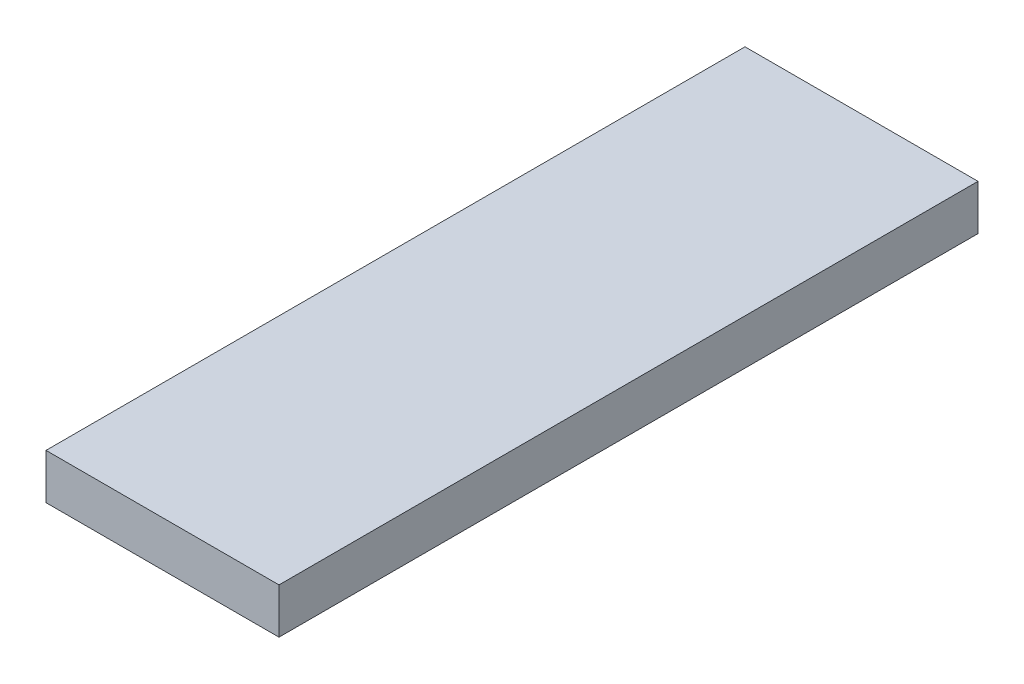
SolidWorks part; units mm, degrees
ref_plane "Plano frontal" through (0, 0, 0) normal (0, 0, 1) x (1, 0, 0)
ref_plane "Plano superior" through (0, 0, 0) normal (0, 1, 0) x (1, 0, 0)
ref_plane "Plano direito" through (0, 0, 0) normal (1, 0, 0) x (0, 0, -1)
sketch "Esboço1" plane through (0, 0, 0) normal (0, 0, 1) x (1, 0, 0)
  line L1 (0, 0) -> (900, 0)
  line L2 (0, 0) -> (0, 175)
  line L3 (0, 175) -> (900, 175)
  line L4 (900, 0) -> (900, 175)
  dimension "D1" = 900
  dimension "D2" = 175
extrude "Ressalto-extrusão1" add sketch "Esboço1" along normal blind 2700
